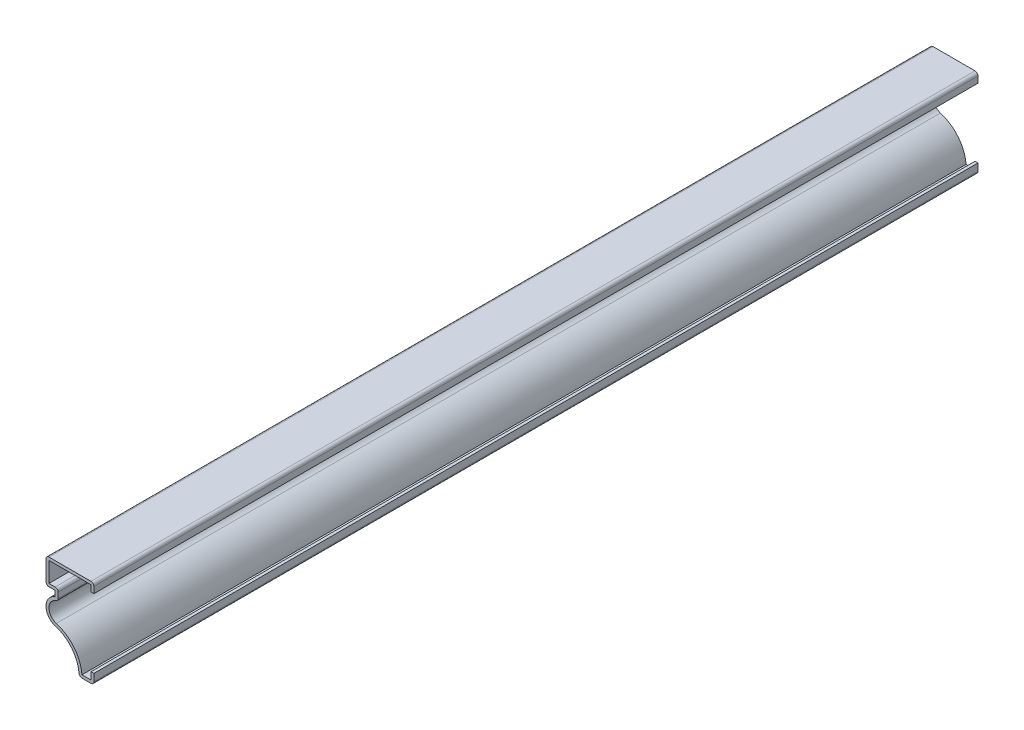
SolidWorks part; units mm, degrees
ref_plane "Front Plane" through (0, 0, 0) normal (0, 0, 1) x (1, 0, 0)
ref_plane "Top Plane" through (0, 0, 0) normal (0, 1, 0) x (1, 0, 0)
ref_plane "Right Plane" through (0, 0, 0) normal (1, 0, 0) x (0, 0, -1)
sketch "Sketch1" plane through (0, 0, 0) normal (0, 0, 1) x (1, 0, 0)
  line L0 (0, 0) -> (0, 38.1) construction
  line L1 (0, 34.1313) -> (0, 38.1)
  line L2 (0, 38.1) -> (-20.6375, 38.1)
  line L3 (-20.6375, 38.1) -> (-20.6375, 26.9875)
  line L4 (-20.6375, 26.9875) -> (-16.6687, 26.9875)
  line L5 (-16.6687, 26.9875) -> (-16.6687, 24.6063)
  line L6 (-6.35, 0) -> (0, 0)
  line L7 (0, 0) -> (0, 4.3656)
  arc A0 (-16.6687, 24.6063) -> (-16.5568, 13.6923) centre (-14.9253, 19.1666) ccw
  arc A1 (-16.5568, 13.6923) -> (-6.35, 0) centre (-20.6375, 0) cw
  point P12 (0, 0)
  point P14 (0, 0)
  point P15 (-15.5517, 19.9896)
  point P16 (-16.6687, 13.7258)
  point P17 (0, 0)
  dimension "D1" = 38.1
  dimension "D2" = 20.6375
  dimension "D3" = 11.1125
  dimension "D4" = 4.3656
  dimension "D5" = 3.9688
  dimension "D6" = 3.9688
  dimension "D7" = 2.3813
  dimension "D8" = 24.6063
  dimension "D9" = 6.35
extrude "Extrude-Thin1" add sketch "Sketch1" against normal blind 381 thin thin type one direction reverse wall 1.27
fillet "Fillet1" radius 1.27 7 edges at (0, 38.1, -190.5) (0, 0, -190.5) (-6.35, 0, -190.5) (-15.3987, 23.5835, -190.5) (-15.3987, 28.2575, -190.5) (-20.6375, 26.9875, -190.5) (-20.6375, 38.1, -190.5)
